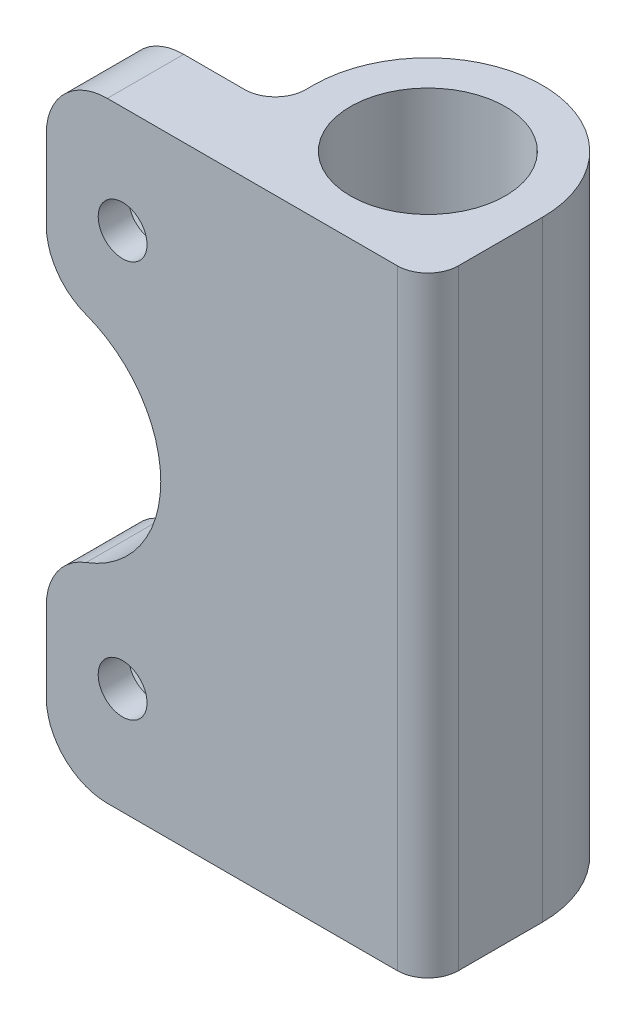
SolidWorks part; units mm, degrees
ref_plane "Alzado" through (0, 0, 0) normal (0, 0, 1) x (1, 0, 0)
ref_plane "Planta" through (0, 0, 0) normal (0, 1, 0) x (1, 0, 0)
ref_plane "Vista lateral" through (0, 0, 0) normal (1, 0, 0) x (0, 0, -1)
sketch "Croquis1" plane through (0, 0, 0) normal (0, 1, 0) x (1, 0, 0)
  line L0 (-17.5, -7.5) -> (7.5, -7.5)
  line L1 (7.5, -7.5) -> (7.5, 0)
  line L2 (-7.5, 0) -> (-7.5, -2.5)
  line L3 (-7.5, -2.5) -> (-17.5, -2.5)
  line L4 (-17.5, -2.5) -> (-17.5, -7.5)
  circle A0 centre (0, 0) radius 5.075
  arc A1 (7.5, 0) -> (-7.5, 0) centre (0, 0) ccw
  dimension "D1" = 10.15
  dimension "D2" = 15
  dimension "D3" = 25
  dimension "D4" = 5
  dimension "D5" = 10
extrude "Saliente-Extruir1" add sketch "Croquis1" along normal blind 40
sketch "Croquis2" plane through (0, 0, 2.5) normal (0, 0, -1) x (-1, 0, 0)
  line L0 (12.5, 40) -> (12.5, 0) construction
  line L1 (7.5, 40) -> (17.5, 40) construction
  line L2 (7.5, 0) -> (17.5, 0) construction
  line L3 (17.5, 20) -> (7.5, 20) construction
  line L4 (17.5, 40) -> (17.5, 0) construction
  line L5 (7.5, 40) -> (7.5, 0) construction
  circle A0 centre (12.5, 7) radius 1.6
  circle A1 centre (12.5, 33) radius 1.6
  dimension "D1" = 3.2
  dimension "D2" = 13
extrude "Cortar-Extruir1" cut sketch "Croquis2" against normal through all
sketch "Croquis3" plane through (0, 0, 2.5) normal (0, 0, -1) x (-1, 0, 0)
  line L0 (7.5, 20) -> (17.5, 20) construction
  line L1 (15.3, 31.3834) -> (15.3, 34.6166)
  line L2 (15.3, 34.6166) -> (12.5, 36.2332)
  line L3 (12.5, 36.2332) -> (9.7, 34.6166)
  line L4 (9.7, 34.6166) -> (9.7, 31.3834)
  line L5 (9.7, 31.3834) -> (12.5, 29.7668)
  line L6 (12.5, 29.7668) -> (15.3, 31.3834)
  line L7 (7.5, 40) -> (7.5, 0) construction
  line L8 (17.5, 40) -> (17.5, 0) construction
  line L9 (12.5, 10.2332) -> (15.3, 8.6166)
  line L10 (9.7, 8.6166) -> (12.5, 10.2332)
  line L11 (9.7, 5.3834) -> (9.7, 8.6166)
  line L12 (12.5, 3.7668) -> (9.7, 5.3834)
  line L13 (15.3, 5.3834) -> (12.5, 3.7668)
  line L14 (15.3, 8.6166) -> (15.3, 5.3834)
  circle A0 centre (12.5, 33) radius 2.8 construction
  circle A1 centre (12.5, 7) radius 2.8 construction
  dimension "D1" = 5.6
extrude "Cortar-Extruir2" cut sketch "Croquis3" against normal blind 3
sketch "Croquis4" plane through (0, 0, 2.5) normal (0, 0, -1) x (-1, 0, 0)
  line L1 (17.5, 40) -> (17.5, 0) construction
  line L2 (17.5, 20) -> (7.5, 20) construction
  line L3 (7.5, 40) -> (7.5, 0) construction
  line L4 (17.5, 27.5) -> (17.5, 12.5)
  arc A0 (17.5, 27.5) -> (17.5, 12.5) centre (17.5, 20) ccw
  dimension "D1" = 15
extrude "Cortar-Extruir3" cut sketch "Croquis4" against normal through all
fillet "Redondeo1" radius 4 4 edges at (-17.5, 0, 5) (-17.5, 12.5, 5) (-17.5, 27.5, 5) (-17.5, 40, 5)
fillet "Redondeo2" radius 2 2 edges at (7.5, 20, 7.5) (-7.5, 20, 2.5)
sketch "Croquis7" plane through (0, 0, 0) normal (0, 0, 1) x (1, 0, 0)
  line L2 (-12.5, 33) -> (-12.5, 40) construction
  line L3 (-9.5, 40) -> (-13.5, 40) construction
